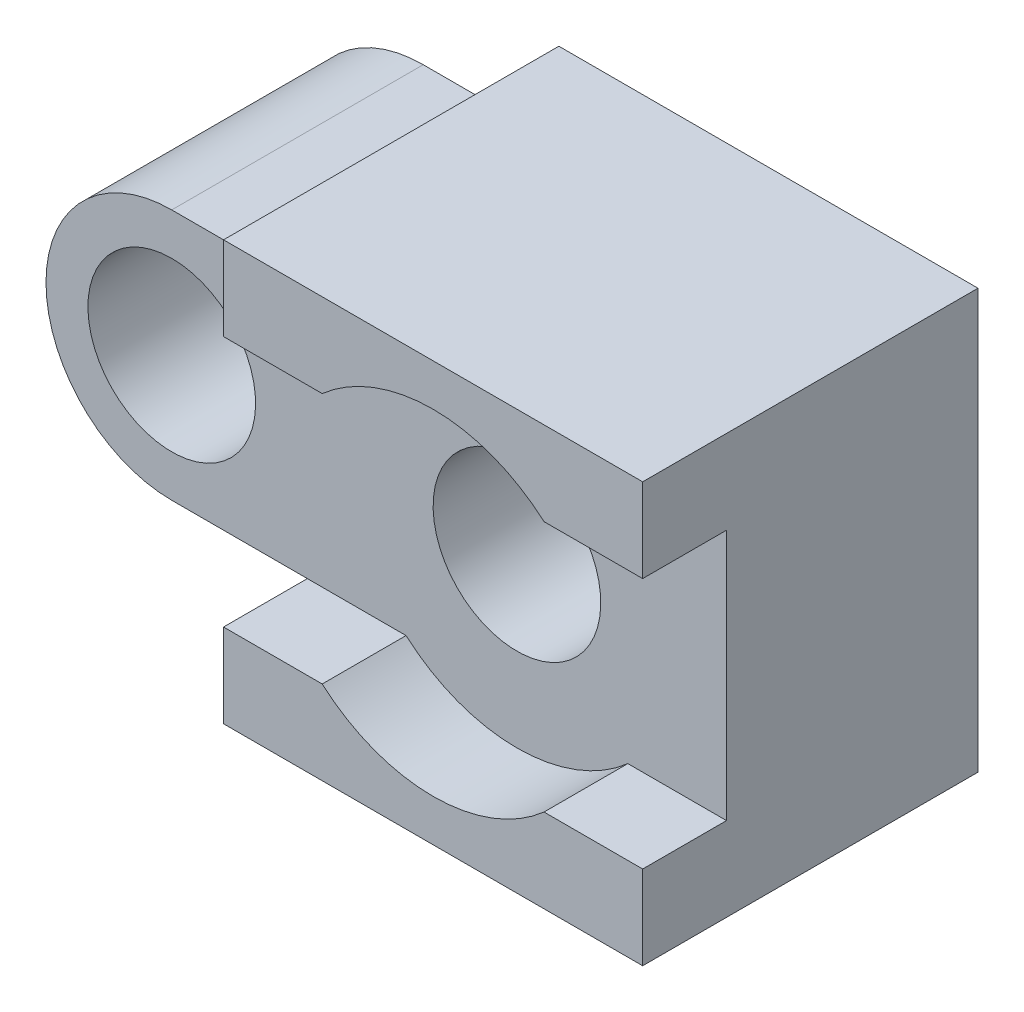
SolidWorks part; units mm, degrees
ref_plane "Front" through (0, 0, 0) normal (0, 0, 1) x (1, 0, 0)
ref_plane "Top" through (0, 0, 0) normal (0, 1, 0) x (1, 0, 0)
ref_plane "Right" through (0, 0, 0) normal (1, 0, 0) x (0, 0, -1)
sketch "Sketch1" plane through (0, 0, 0) normal (0, 0, 1) x (1, 0, 0)
  line L0 (-5, 3) -> (-8.2356, 3)
  line L1 (-5, -5) -> (5, -5)
  line L2 (-5, -5) -> (-5, -3)
  line L3 (-5, 5) -> (5, 5)
  line L4 (5, -5) -> (5, 5)
  line L5 (-5, -5) -> (5, 5) construction
  line L6 (-5, 5) -> (5, -5) construction
  line L7 (-5, -3) -> (-8.2356, -3)
  line L8 (-5, 3) -> (-5, 5)
  arc A0 (-8.2356, 3) -> (-11.2356, -0.0064) centre (-8.2356, 0) ccw
  circle A1 centre (-8.2356, 0) radius 2
  arc A2 (-8.2356, -3) -> (-11.2356, -0.0064) centre (-8.2356, 0) cw
  circle A3 centre (0, 0) radius 2
  point P0 (0, 0)
  dimension "D4" = 3
  dimension "D5" = 6
  dimension "D6" = 3
  dimension "D7" = 4
  dimension "D1" = 10
  dimension "D2" = 10
extrude "Boss-Extrude1" add sketch "Sketch1" along normal blind 8
sketch "Sketch2" plane through (0, 0, 0) normal (1, 0, 0) x (0, 0, -1)
  line L0 (-8, -3) -> (0, -3) construction
  line L1 (-8, 3) -> (-6, 3)
  line L2 (-8, 3) -> (-8, -3)
  line L3 (-8, -3) -> (-6, -3)
  line L4 (-6, 3) -> (-6, -3)
  dimension "D1" = 2
extrude "Cut-Extrude1" cut sketch "Sketch2" against normal mid plane 36
sketch "Sketch3" plane through (0, 0, 6) normal (0, 0, 1) x (1, 0, 0)
  circle A0 centre (0, 0) radius 4
  dimension "D1" = 8
extrude "Cut-Extrude2" cut sketch "Sketch3" along normal blind 36
